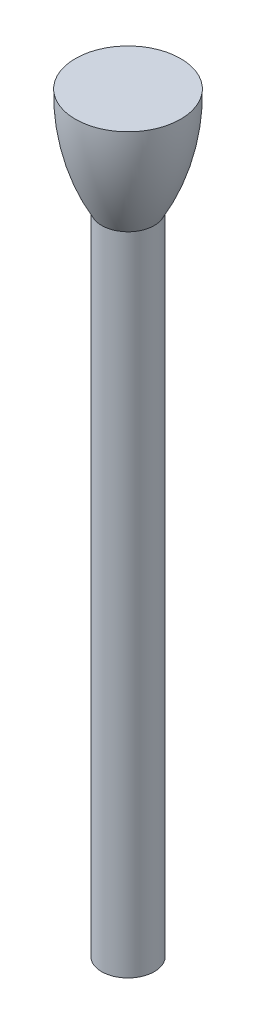
SolidWorks part; units mm, degrees
ref_plane "Front Plane" through (0, 0, 0) normal (0, 0, 1) x (1, 0, 0)
ref_plane "Top Plane" through (0, 0, 0) normal (0, 1, 0) x (1, 0, 0)
ref_plane "Right Plane" through (0, 0, 0) normal (1, 0, 0) x (0, 0, -1)
sketch "Sketch1" plane through (0, 0, 0) normal (0, 1, 0) x (1, 0, 0)
  circle A0 centre (0, 0) radius 11.1125
  dimension "D1" = 22.225
extrude "Boss-Extrude1" add sketch "Sketch1" along normal mid plane 273.05
sketch "Sketch3" plane through (0, 0, 0) normal (0, 0, 1) x (1, 0, 0)
  line L0 (0, 136.525) -> (0, 180.975)
  line L1 (11.1125, 136.525) -> (-11.1125, 136.525) construction
  line L2 (0, 180.975) -> (-22.225, 180.975)
  line L3 (-11.1125, 136.525) -> (0, 136.525)
  arc A0 (-22.225, 180.975) -> (-11.1125, 136.525) centre (65.8591, 179.382) ccw
  dimension "D3" = 88.0985
  dimension "D1" = 44.45
  dimension "D2" = 22.225
revolve "Revolve1" add sketch "Sketch3" angle 360 about L0
